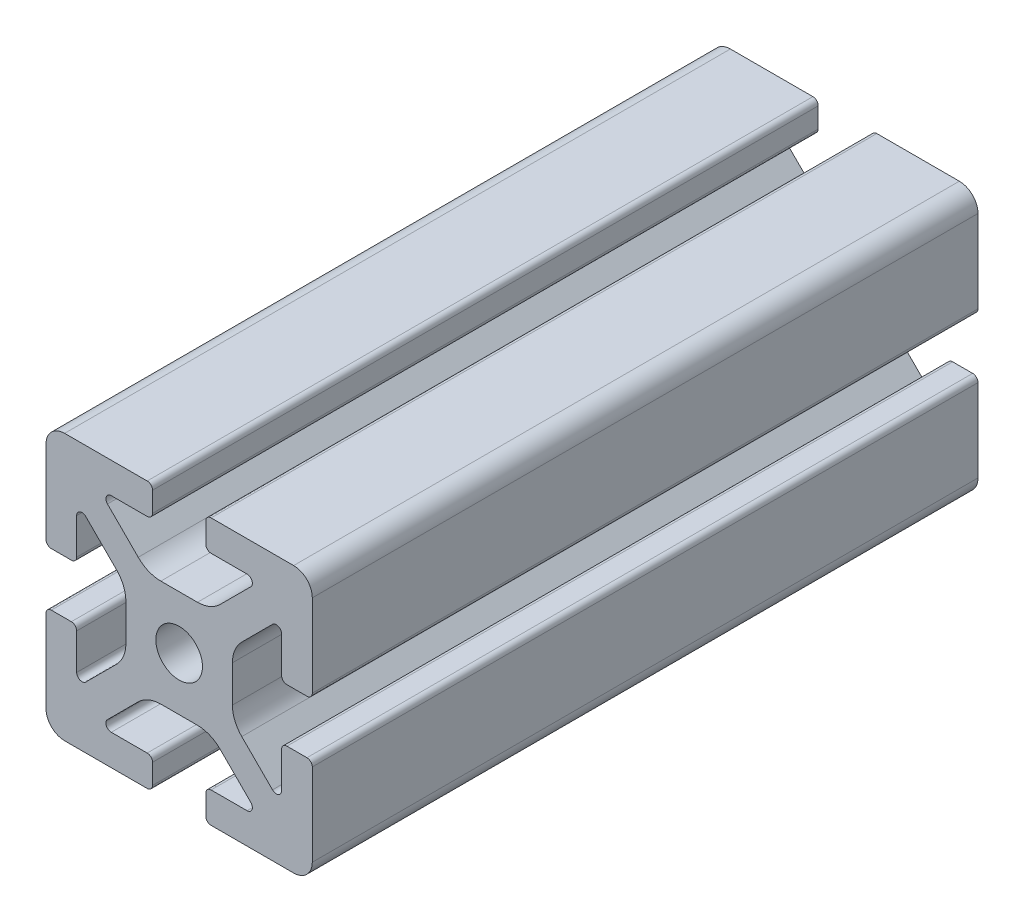
SolidWorks part; units mm, degrees
material "6061-T6 (SS)"
ref_plane "Front Plane" through (0, 0, 0) normal (0, 0, 1) x (1, 0, 0)
ref_plane "Top Plane" through (0, 0, 0) normal (0, 1, 0) x (1, 0, 0)
ref_plane "Right Plane" through (0, 0, 0) normal (1, 0, 0) x (0, 0, -1)
sketch "Sketch2" plane through (0, 0, 0) normal (0, 0, 1) x (1, 0, 0)
  line L0 (0, 20) -> (0, -20) construction
  line L1 (-20, 0) -> (20, 0) construction
  line L2 (4, -20) -> (20, -20)
  line L3 (20, -20) -> (20, -4)
  line L4 (4, -20) -> (4, -15.3907)
  line L5 (4, -15.3907) -> (12.1314, -15.3907)
  line L6 (12.1314, -15.3907) -> (4.7407, -8)
  line L7 (0, 0) -> (20, -20) construction
  line L8 (20, -4) -> (15.3907, -4)
  line L9 (15.3907, -4) -> (15.3907, -12.1314)
  line L10 (15.3907, -12.1314) -> (8, -4.7407)
  line L11 (11.6953, -8.436) -> (8.436, -11.6953) construction
  circle A0 centre (0, 0) radius 3.5
  arc A1 (10.2, -15.3907) -> (10.7657, -14.025) centre (10.2, -14.5907) ccw construction
  point P8 (0, -8)
  point P16 (10.0657, -10.0657)
  dimension "Center Hole Diameter" = 7
  dimension "D3" = 0.8
  dimension "Rail Height" = 40
  dimension "Rail Width" = 40
  dimension "T-Slot Width" = 8
  dimension "Slot Depth" = 12
  dimension "Slot Inner Width" = 22
sketch "Sketch3" plane through (0, 0, 0) normal (1, 0, 0) x (0, 0, -1)
  line L0 (-457.2, -20) -> (457.2, -20) construction
  line L1 (-431.8, 0) -> (431.8, 0) construction
  line L2 (0, 20) -> (0, -20) construction
  line L3 (0, 20) -> (0, -20) construction
  point P6 (-431.8, 0)
  point P8 (431.8, 0)
  dimension "Length" = 914.4
  dimension "D1" = 25.4
sketch "Sketch4" plane through (0, 0, 0) normal (0, 0, 1) x (1, 0, 0)
  line L0 (4.8, -20) -> (17.2, -20)
  line L1 (4, -20) -> (20, -20) construction
  line L2 (4, -20) -> (4, -15.3907) construction
  line L3 (4, -15.3907) -> (12.1314, -15.3907) construction
  line L4 (4, -16.1907) -> (4, -19.2)
  line L5 (4.8, -15.3907) -> (10.2, -15.3907)
  line L6 (0, -8) -> (2.7525, -8)
  line L7 (12.1314, -15.3907) -> (4.7407, -8) construction
  line L8 (6.1466, -9.4059) -> (10.7657, -14.025)
  line L9 (20, -20) -> (20, -4) construction
  line L10 (15.3907, -12.1314) -> (8, -4.7407) construction
  line L11 (15.3907, -4) -> (15.3907, -12.1314) construction
  line L12 (15.3907, -10.2) -> (15.3907, -4.8)
  line L13 (20, -4) -> (15.3907, -4) construction
  line L14 (16.1907, -4) -> (19.2, -4)
  line L15 (20, -4.8) -> (20, -17.2)
  line L16 (14.025, -10.7657) -> (9.4059, -6.1466)
  line L17 (8, 0) -> (8, -2.7525)
  line L18 (-20, 0) -> (20, 0) construction
  line L19 (0, -8) -> (0, -3.5)
  line L20 (0, 20) -> (0, -20) construction
  line L21 (8, 0) -> (3.5, 0)
  arc A0 (4, -19.2) -> (4.8, -20) centre (4.8, -19.2) ccw
  arc A1 (10.2, -15.3907) -> (10.7657, -14.025) centre (10.2, -14.5907) ccw construction
  arc A2 (4, -16.1907) -> (4.8, -15.3907) centre (4.8, -16.1907) cw
  arc A3 (10.2, -15.3907) -> (10.7657, -14.025) centre (10.2, -14.5907) ccw
  arc A4 (2.7525, -8) -> (6.1466, -9.4059) centre (2.7525, -12.8) cw
  arc A5 (17.2, -20) -> (20, -17.2) centre (17.2, -17.2) ccw
  arc A6 (14.025, -10.7657) -> (15.3907, -10.2) centre (14.5907, -10.2) ccw
  arc A7 (15.3907, -4.8) -> (16.1907, -4) centre (16.1907, -4.8) cw
  arc A8 (19.2, -4) -> (20, -4.8) centre (19.2, -4.8) cw
  arc A9 (9.4059, -6.1466) -> (8, -2.7525) centre (12.8, -2.7525) cw
  circle A10 centre (0, 0) radius 3.5 construction
  arc A11 (0, -3.5) -> (3.5, 0) centre (0, 0) ccw
  dimension "D1" = 2.8
  dimension "D2" = 4.8
extrude "Boss-Extrude1" add sketch "Sketch4" along normal mid plane 100
mirror "Mirror1" about plane through (0, 0, 0) normal (1, 0, 0) of bodies 134
mirror "Mirror2" about plane through (0, 0, 0) normal (0, 1, 0) of bodies 135
equation "\"D3@Sketch2\"=\"T-Slot Width@Sketch2\"*0.1"
equation "\"D1@Sketch4\"=\"D3@Sketch2\"*3.5"
equation "\"D2@Sketch4\"=\"D3@Sketch2\"*6"
equation "\"D1@Boss-Extrude1\"=\"Length@Sketch3\""
